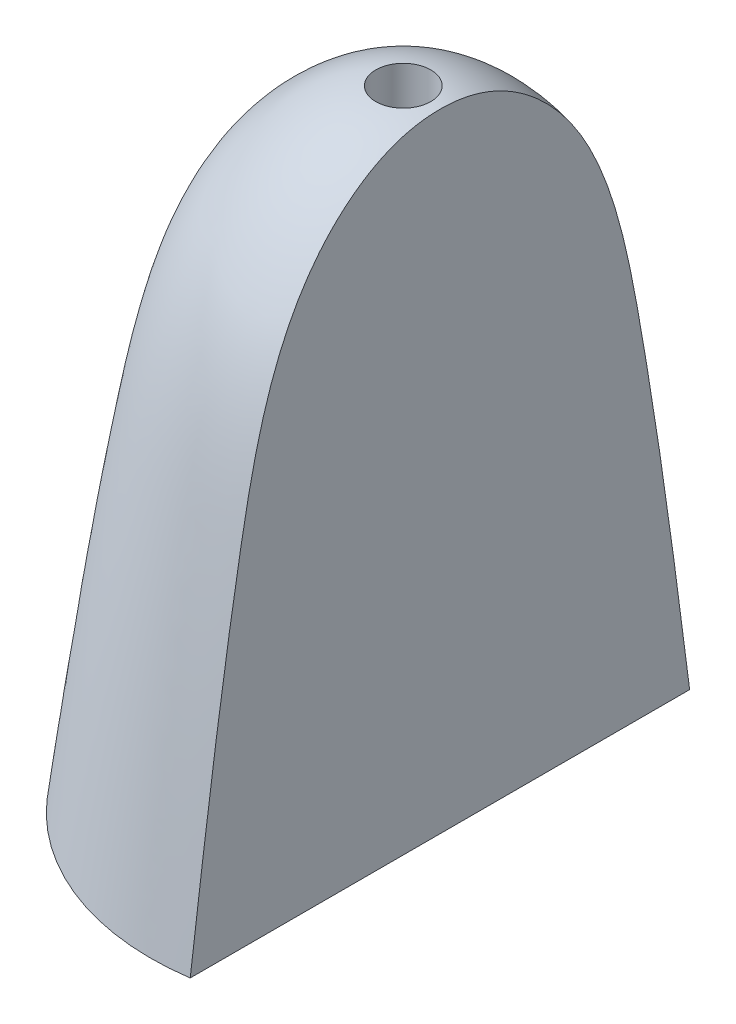
SolidWorks part; units mm, degrees
ref_plane "Plan de face" through (0, 0, 0) normal (0, 0, 1) x (1, 0, 0)
ref_plane "Plan de dessus" through (0, 0, 0) normal (0, 1, 0) x (1, 0, 0)
ref_plane "Plan de droite" through (0, 0, 0) normal (1, 0, 0) x (0, 0, -1)
sketch "Sketch1" plane through (0, 0, 0) normal (0, 0, 1) x (1, 0, 0)
  line L0 (0, 18.0579) -> (0, 5.5898) construction
  line L1 (4.88, 0) -> (6.88, 0)
  line L2 (0, 17.2) -> (0, 15.4)
  arc A0 (4.88, 0) -> (4.88, 1.6062) centre (-7.5884, 0.8031) ccw
  spline S0 degree 3 poles (6.88, 0) (6.4769, 3.1777) (5.8089, 8.3578) (4.3783, 15.4646) (1.1111, 17.2802) (0, 17.2) knots 0 0 0 0 0.473755 0.838492 1 1 1 1
  spline S1 degree 2 poles (0, 15.4) (1.563, 15.2978) (2.2842, 13.6332) knots 0 0 0 1 1 1
  spline S2 degree 2 poles (2.2842, 13.6332) (4.2663, 7.7784) (4.88, 1.6062) knots 0 0 0 1 1 1
  dimension "D4" = 2
  dimension "D1" = 15.4
  dimension "D2" = 2
  dimension "D3" = 1.8
  dimension "D5" = 4.88
revolve "Revolve1" add sketch "Sketch1" angle 360 about L0
sketch "Sketch2" plane through (0, 0, 0) normal (0, 1, 0) x (1, 0, 0)
  circle A1 centre (0, 0) radius 0.5
extrude "Cut-Extrude2" cut sketch "Sketch2" along normal through all
sketch3d "3DSketch1"
  point P0 (-2.2452, 9.2133, -5.0907)
ref_plane "Plane2" through (7, 0, 0) normal (1, 0, 0) x (0, 0, -1)
sketch "Sketch5" plane through (0, 0, 0) normal (0, -1, 0) x (1, 0, 0)
  line L1 (2, 9.912) -> (7, 9.912)
  line L2 (2, 9.912) -> (2, -8.088)
  line L3 (2, -8.088) -> (7, -8.088)
  line L4 (7, 9.912) -> (7, -8.088)
  line L5 (2, 9.912) -> (7, -8.088) construction
  line L6 (2, -8.088) -> (7, 9.912) construction
  circle A0 centre (0, 0) radius 6.88 construction
  point P0 (4.5, 0.912)
  dimension "D1" = 2
  dimension "D2" = 18
  dimension "D3" = 5
extrude "Cut-Extrude4" cut sketch "Sketch5" against normal blind 20
sketch "Sketch9" plane through (0, 0, 0) normal (0, 0, 1) x (1, 0, 0)
  line L0 (0, 17.2) -> (0, 0)
  line L1 (4.88, 0) -> (6.88, 0)
  line L3 (0, 0) -> (4.88, 0)
  spline S0 degree 3 poles (6.88, 0) (6.4769, 3.1777) (5.8089, 8.3578) (4.3783, 15.4646) (1.1111, 17.2802) (0, 17.2) knots 0 0 0 0 0.473755 0.838492 1 1 1 1
  dimension "D2" = 2
revolve "Revolve3" add sketch "Sketch9" angle 90 about L0
ref_plane "Plane4" through (10, 0, 0) normal (1, 0, 0) x (0, 0, -1)
sketch "Sketch12" plane through (10, 0, 0) normal (1, 0, 0) x (0, 0, -1)
  line L1 (-7.579, 18.113) -> (7.579, 18.113)
  line L2 (-7.579, 18.113) -> (-7.579, -0.8499)
  line L3 (-7.579, -0.8499) -> (7.579, -0.8499)
  line L4 (7.579, 18.113) -> (7.579, -0.8499)
  line L5 (-7.579, 18.113) -> (7.579, -0.8499) construction
  line L6 (-7.579, -0.8499) -> (7.579, 18.113) construction
  point P0 (0, 8.6315)
extrude "Cut-Extrude5" cut sketch "Sketch12" against normal blind 9
ref_plane "Plane5" through (0, 20, 0) normal (0, 1, 0) x (1, 0, 0)
sketch "Sketch14" plane through (0, 20, 0) normal (0, 1, 0) x (1, 0, 0)
  circle A0 centre (0, 0) radius 0.5
  dimension "D1" = 1
extrude "Cut-Extrude6" cut sketch "Sketch14" against normal blind 6
sketch "Sketch15" plane through (0, 20, 0) normal (0, 1, 0) x (1, 0, 0)
  circle A0 centre (0, 0) radius 0.75
  dimension "D1" = 1.5
extrude "Cut-Extrude7" cut sketch "Sketch15" against normal blind 7
